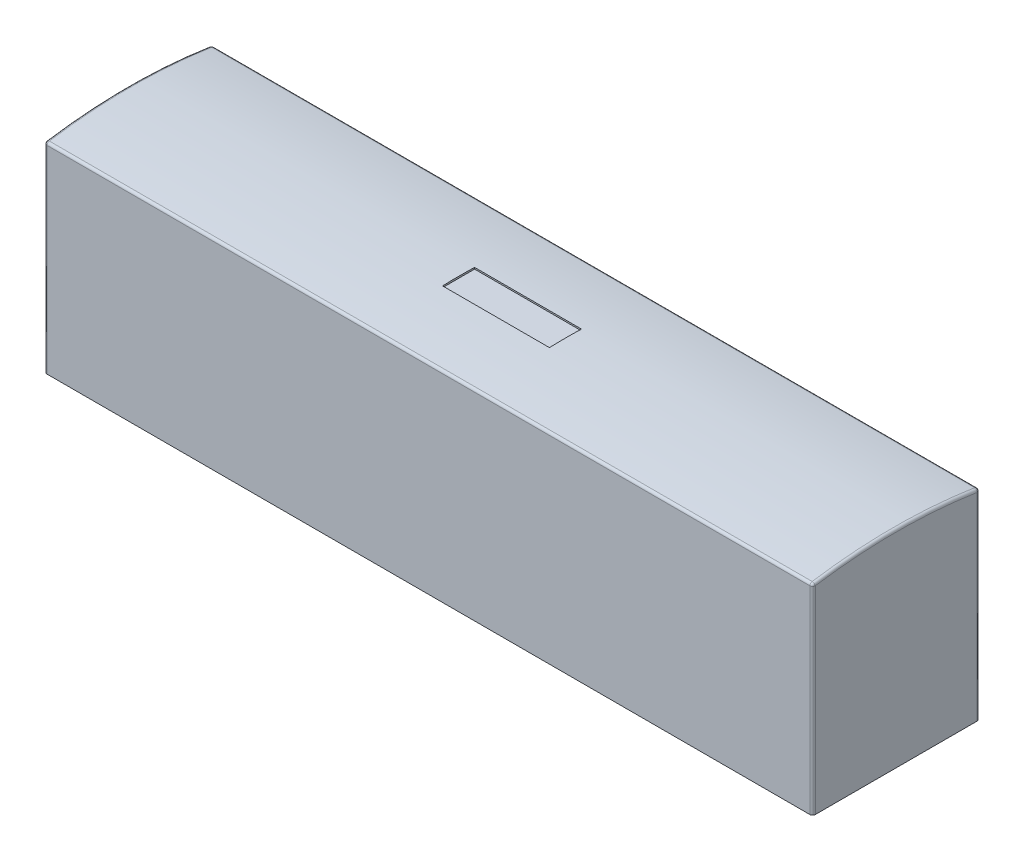
SolidWorks part; units mm, degrees
material "PE High Density"
ref_plane "Front Plane" through (0, 0, 0) normal (0, 0, 1) x (1, 0, 0)
ref_plane "Top Plane" through (0, 0, 0) normal (0, 1, 0) x (1, 0, 0)
ref_plane "Right Plane" through (0, 0, 0) normal (1, 0, 0) x (0, 0, -1)
sketch "Sketch1" plane through (0, 0, 0) normal (0, 1, 0) x (1, 0, 0)
  line L1 (0, 0) -> (18.2562, 0)
  line L2 (0, 0) -> (0, 3.9688)
  line L3 (0, 3.9688) -> (18.2562, 3.9688)
  line L4 (18.2562, 0) -> (18.2562, 3.9688)
  dimension "D1" = 18.2562
  dimension "D2" = 3.9688
extrude "Boss-Extrude1" add sketch "Sketch1" along normal blind 4.7625
sketch "Sketch2" plane through (18.2562, 0, 0) normal (1, 0, 0) x (0, 0, -1)
  line L0 (0, 4.7625) -> (3.9688, 4.7625)
  arc A0 (3.9688, 4.7625) -> (0, 4.7625) centre (1.9844, -7.7815) ccw
  dimension "D1" = 12.7
extrude "Boss-Extrude2" add sketch "Sketch2" against normal up to surface (18.2562 mm away) up to face at (0, 2.3813, -1.9844)
ref_plane "Plane1" through (0, 4.8768, 0) normal (0, 1, 0) x (1, 0, 0)
sketch "Sketch4" plane through (0, 4.8768, 0) normal (0, 1, 0) x (1, 0, 0)
  line L0 (0, 1.9844) -> (18.2562, 1.9844) construction
  line L1 (7.8581, 1.6034) -> (10.3981, 1.6034)
  line L2 (7.8581, 1.6034) -> (7.8581, 2.3654)
  line L3 (7.8581, 2.3654) -> (10.3981, 2.3654)
  line L4 (10.3981, 1.6034) -> (10.3981, 2.3654)
  line L5 (7.8581, 1.6034) -> (10.3981, 2.3654) construction
  line L6 (7.8581, 2.3654) -> (10.3981, 1.6034) construction
  point P0 (9.1281, 1.9844)
  point P5 (9.6528, 2.3175)
  point P6 (0, 0)
  dimension "D1" = 0.762
  dimension "D2" = 2.54
extrude "Cut-Extrude1" cut sketch "Sketch4" along normal through all
fillet "Fillet1" radius 0.0635 8 edges at (0, 4.9185, -1.9844) (18.2562, 4.9185, -1.9844) (9.1281, 4.7625, -3.9688) (9.1281, 4.7625, 0) (0, 2.3812, 0) (0, 2.3813, -3.9688) (18.2562, 2.3813, -3.9688) (18.2562, 2.3813, 0)
